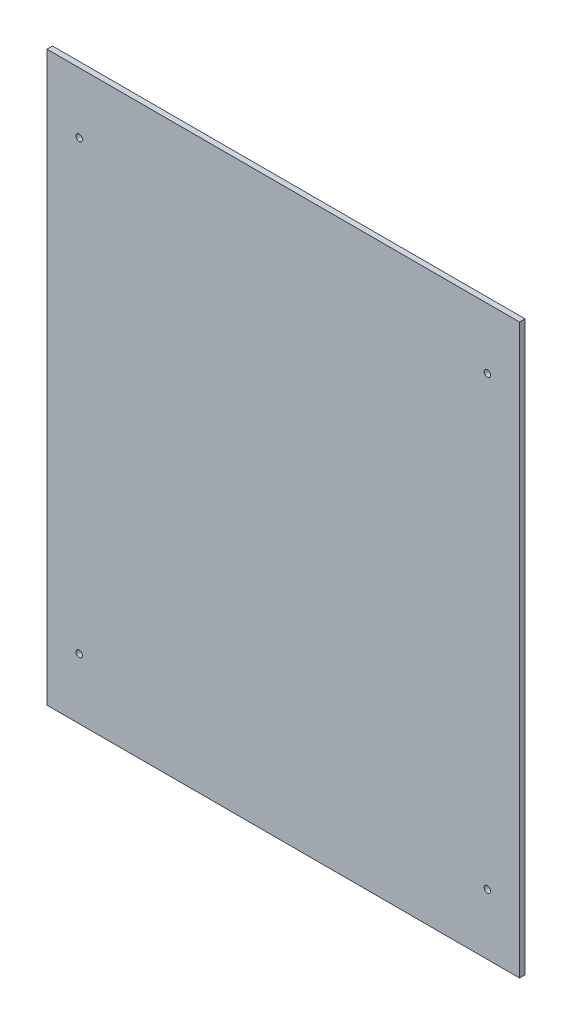
SolidWorks part; units mm, degrees
ref_plane "Plan de face" through (0, 0, 0) normal (0, 0, 1) x (1, 0, 0)
ref_plane "Plan de dessus" through (0, 0, 0) normal (0, 1, 0) x (1, 0, 0)
ref_plane "Plan de droite" through (0, 0, 0) normal (1, 0, 0) x (0, 0, -1)
sketch "Esquisse1" plane through (0, 0, 0) normal (0, 0, 1) x (1, 0, 0)
  line L0 (0, 154.5) -> (0, -154.5) construction
  line L1 (128.5, 154.5) -> (-128.5, 154.5)
  line L2 (128.5, 154.5) -> (128.5, -154.5)
  line L3 (128.5, -154.5) -> (-128.5, -154.5)
  line L4 (-128.5, 154.5) -> (-128.5, -154.5)
  line L5 (128.5, 154.5) -> (-128.5, -154.5) construction
  line L6 (128.5, -154.5) -> (-128.5, 154.5) construction
  line L7 (-111, 121.5) -> (0, 121.5) construction
  line L8 (-128.5, 0) -> (128.5, 0) construction
  circle A0 centre (-111, 121.5) radius 1.75
  circle A1 centre (111, 121.5) radius 1.75
  circle A2 centre (111, -121.5) radius 1.75
  circle A3 centre (-111, -121.5) radius 1.75
  point P0 (0, 0)
  dimension "D3" = 3.5
  dimension "D1" = 257
  dimension "D2" = 309
  dimension "D4" = 111
  dimension "D5" = 33
extrude "Boss.-Extru.1" add sketch "Esquisse1" along normal blind 3
